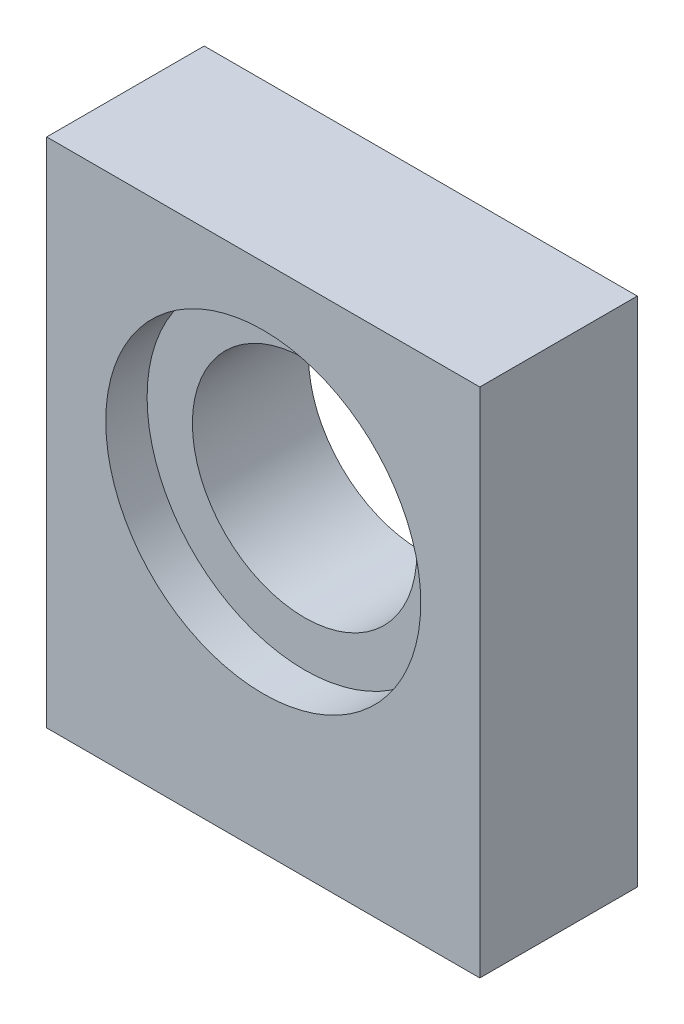
SolidWorks part; units mm, degrees
ref_plane "Front Plane" through (0, 0, 0) normal (0, 0, 1) x (1, 0, 0)
ref_plane "Top Plane" through (0, 0, 0) normal (0, 1, 0) x (1, 0, 0)
ref_plane "Right Plane" through (0, 0, 0) normal (1, 0, 0) x (0, 0, -1)
sketch "Sketch1" plane through (0, 0, 0) normal (0, 0, 1) x (1, 0, 0)
  line L1 (0, 0) -> (22, 0)
  line L2 (0, 0) -> (0, 26)
  line L3 (0, 26) -> (22, 26)
  line L4 (22, 0) -> (22, 26)
  circle A0 centre (11, 15) radius 5.7
  dimension "D5" = 11.4
  dimension "D1" = 22
  dimension "D2" = 26
  dimension "D3" = 11
  dimension "D4" = 15
extrude "Boss-Extrude1" add sketch "Sketch1" along normal blind 8
sketch "Sketch3" plane through (0, 0, 8) normal (0, 0, -1) x (-1, 0, 0)
  circle A0 centre (-11, 15) radius 8
  dimension "D1" = 16
extrude "Cut-Extrude2" cut sketch "Sketch3" along normal blind 2.1
hole_wizard "Tap Drill for M3x0.5 Tap1" positions "Sketch5" profile "Sketch4" hole size "M3x0.5" standard "ANSI Metric"
sketch "Sketch5" plane through (0, 0, 0) normal (0, -1, 0) x (-1, 0, 0)
  line L0 (0, 0) -> (-22, 0) construction
  line L3 (-18, -2.5) -> (-4, -2.5) construction
  line L4 (-18, -2.5) -> (-18, -5.5) construction
  line L5 (-18, -5.5) -> (-4, -5.5) construction
  line L6 (-4, -2.5) -> (-4, -5.5) construction
  line L7 (0, -8) -> (-22, -8) construction
  line L8 (0, -8) -> (0, 0) construction
  line L9 (-22, -8) -> (-22, 0) construction
  point P4 (-4, -5.5)
  point P6 (-18, -5.5)
  point P8 (-11, -2.5)
  dimension "D2" = 4
  dimension "D3" = 2.5
  dimension "D4" = 2.5
  dimension "D6" = 4
sketch "Sketch4" plane through (4, 0, 5.5) normal (1, 0, 0) x (0, 0, -1)
  line L0 (0, 0) -> (0, 5.7511)
  line L1 (0, 5.7511) -> (1.25, 5)
  line L2 (1.25, 5) -> (1.25, 0)
  line L5 (1.25, 0) -> (0, 0)
  line L10 (0, 5.7511) -> (-1.25, 5) construction
  line L11 (0, -6.35) -> (0, 107.95) construction
  dimension "Hole Dia." = 2.5
  dimension "Hole Depth" = 5
  dimension "Drill Angle" = 118
